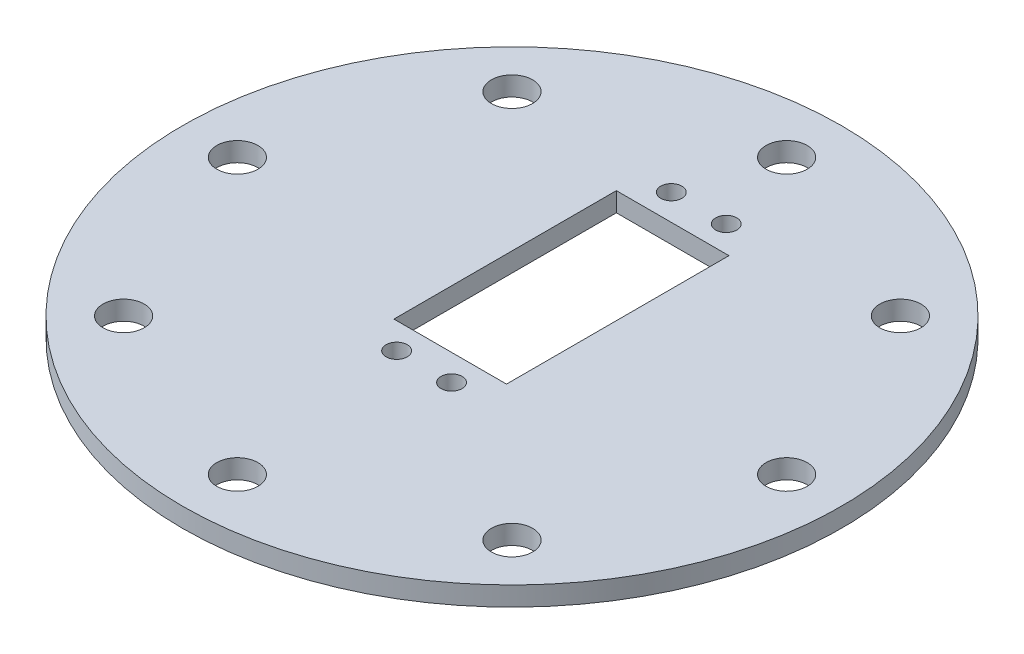
SolidWorks part; units mm, degrees
material "Balsa"
ref_plane "Alzado" through (0, 0, 0) normal (0, 0, 1) x (1, 0, 0)
ref_plane "Planta" through (0, 0, 0) normal (0, 1, 0) x (1, 0, 0)
ref_plane "Vista lateral" through (0, 0, 0) normal (1, 0, 0) x (0, 0, -1)
sketch "Croquis1" plane through (0, 0, 0) normal (0, 1, 0) x (1, 0, 0)
  circle A0 centre (0, 0) radius 60
extrude "Saliente-Extruir1" add sketch "Croquis1" along normal blind 3.5 contours A0
sketch "Croquis2" plane through (0, 3.5, 0) normal (0, 1, 0) x (1, 0, 0)
  circle A0 centre (0, 50) radius 3.75
  dimension "D1" = 50
  dimension "D2" = 7.5
extrude "Cortar-Extruir1" cut sketch "Croquis2" against normal up to next (3.5 mm away)
pattern_circular "MatrizC1" count 8 over 360 about axis through (0, 0, 0) along (0, 1, 0) of "Cortar-Extruir1"
sketch "Croquis3" plane through (0, 3.5, 0) normal (0, 1, 0) x (1, 0, 0)
  line L1 (-10.25, 20.25) -> (10.25, 20.25)
  line L2 (-10.25, 20.25) -> (-10.25, -20.25)
  line L3 (-10.25, -20.25) -> (10.25, -20.25)
  line L4 (10.25, 20.25) -> (10.25, -20.25)
  line L5 (-10.25, 20.25) -> (10.25, -20.25) construction
  line L6 (-10.25, -20.25) -> (10.25, 20.25) construction
  point P0 (0, 0)
  point P6 (0, 9)
  dimension "D1" = 40.5
  dimension "D2" = 20.5
  dimension "D3" = 9
sketch "Croquis4" plane through (0, 3.5, 0) normal (0, 1, 0) x (1, 0, 0)
  line L0 (0, 9) -> (0, 14.9401) construction
  line L1 (0, 14.9401) -> (0, 9) construction
  line L2 (0, 9) -> (-4.5556, 9) construction
  line L3 (-10.25, 20.25) -> (10.25, -20.25) construction
  line L4 (-4.5556, 9) -> (4.5556, 9) construction
  line L5 (-10.25, -20.25) -> (10.25, 20.25) construction
  line L6 (4.5556, 9) -> (0, 9) construction
  line L7 (0, 9) -> (0, 4.2212) construction
  circle A4 centre (5, 34) radius 1.9264
  circle A6 centre (5, -16) radius 1.9264
  circle A7 centre (-5, 34) radius 1.9264
  circle A8 centre (-5, -16) radius 1.9264
  dimension "D1" = 25
  dimension "D2" = 5
extrude "Cortar-Extruir3" cut sketch "Croquis4" against normal up to next
sketch "Croquis5" plane through (0, 3.5, 0) normal (0, 1, 0) x (1, 0, 0)
  line L0 (10.25, 20.25) -> (10.25, -20.25) construction
  line L1 (-10.25, 29.25) -> (10.25, 29.25)
  line L2 (-10.25, 29.25) -> (-10.25, -11.25)
  line L3 (-10.25, -11.25) -> (10.25, -11.25)
  line L4 (10.25, 29.25) -> (10.25, -11.25)
  line L5 (-10.25, 29.25) -> (10.25, -11.25) construction
  line L6 (-10.25, -11.25) -> (10.25, 29.25) construction
  point P0 (0, 9)
  dimension "D1" = 40.5
extrude "Cortar-Extruir4" cut sketch "Croquis5" against normal up to next
